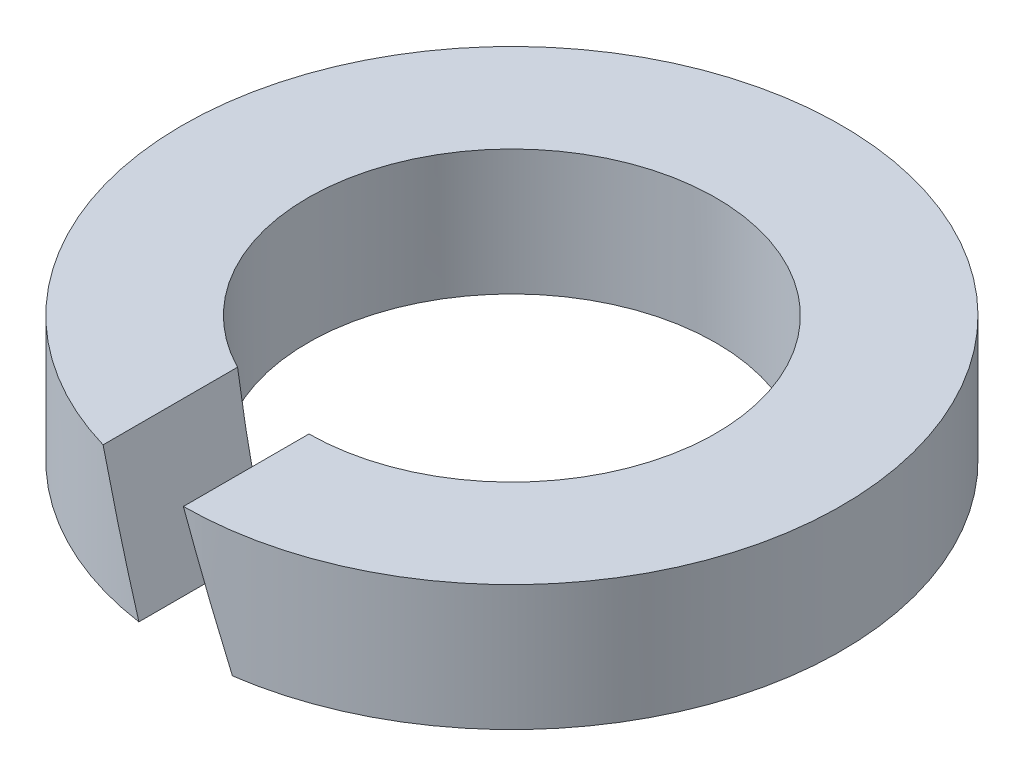
SolidWorks part; units mm, degrees
ref_plane "Спереди" through (0, 0, 0) normal (0, 0, 1) x (1, 0, 0)
ref_plane "Сверху" through (0, 0, 0) normal (0, 1, 0) x (1, 0, 0)
ref_plane "Справа" through (0, 0, 0) normal (1, 0, 0) x (0, 0, -1)
sketch "Ske" plane through (0, 0, 0) normal (0, 0, 1) x (1, 0, 0)
  line L0 (0, 15.7597) -> (0, -13.7032) construction
  line L1 (-1.3, 0) -> (-2.1, 0)
  line L2 (-1.3, 0) -> (-1.3, 0.8)
  line L3 (-1.3, 0.8) -> (-2.1, 0.8)
  line L4 (-2.1, 0) -> (-2.1, 0.8)
  dimension "S" = 0.8
  dimension "H" = 0.8
  dimension "Insid_Dia" = 2.6
revolve "Base" add sketch "Ske" angle 360 about L0
sketch "Ske4" plane through (0, 0, 0) normal (0, 0, 1) x (1, 0, 0)
  line L0 (0, 0) -> (-0.6869, 1.8873) construction
  line L1 (-1.3, 0) -> (1.3, 0) construction
  line L2 (1.3, 0.8) -> (-1.3, 0.8) construction
  line L3 (-0.298, 0) -> (0.298, 0)
  line L4 (0.0068, 0.8) -> (-0.5891, 0.8)
  line L5 (0.0068, 0.8) -> (0.298, 0)
  line L6 (-0.5891, 0.8) -> (-0.298, 0)
  dimension "D1" = 110
  dimension "D2" = 0.56
extrude "Cut" cut sketch "Ske4" along normal up to next
equation "\"D2@Ske4\"=0.7*\"H@Ske\""
